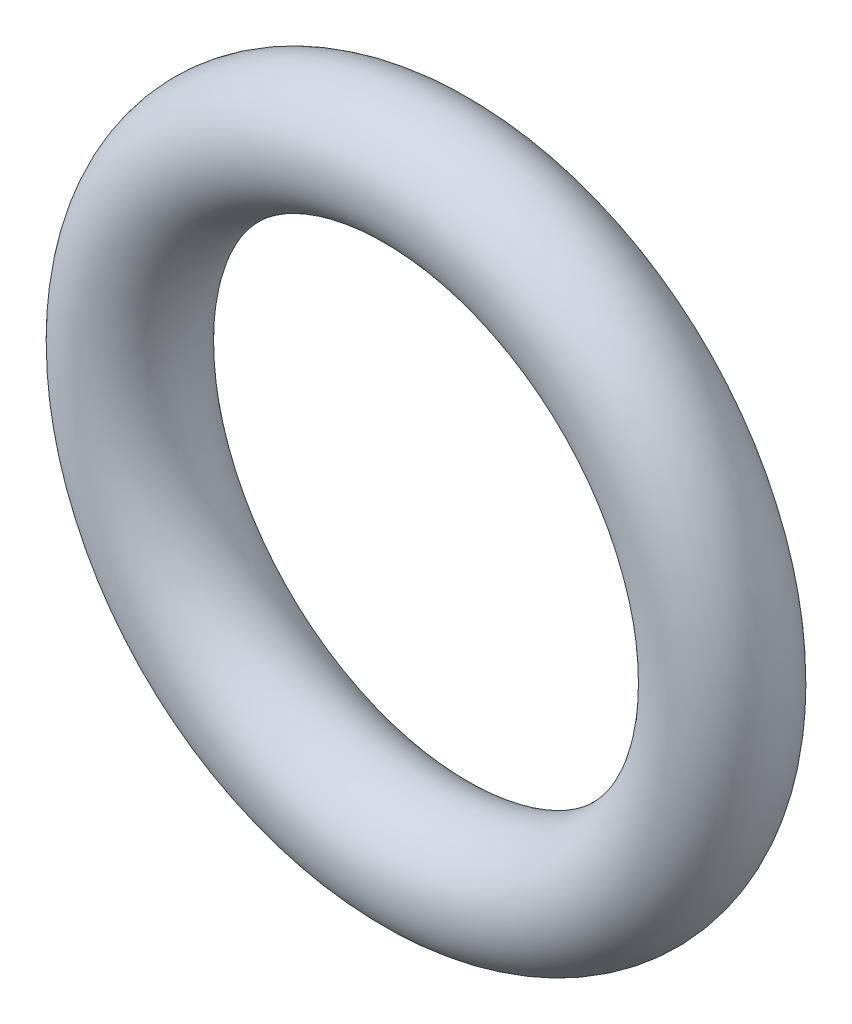
SolidWorks part; units mm, degrees
ref_plane "Front Plane" through (0, 0, 0) normal (0, 0, 1) x (1, 0, 0)
ref_plane "Top Plane" through (0, 0, 0) normal (0, 1, 0) x (1, 0, 0)
ref_plane "Right Plane" through (0, 0, 0) normal (1, 0, 0) x (0, 0, -1)
sketch "Sketch1" plane through (0, 0, 0) normal (0, 0, 1) x (1, 0, 0)
  circle A0 centre (0, 0) radius 5.08
  point P3 (5.08, 0)
sketch "Sketch2" plane through (0, 0, 0) normal (0, 1, 0) x (1, 0, 0)
  circle A0 centre (5.08, 0) radius 1.016
sweep "Sweep1" add profiles "Sketch2" path "Sketch1"
sketch "Sketch3" plane through (0, 0, 0) normal (0, 0, 1) x (1, 0, 0)
  circle A0 centre (0, 0) radius 4.064
